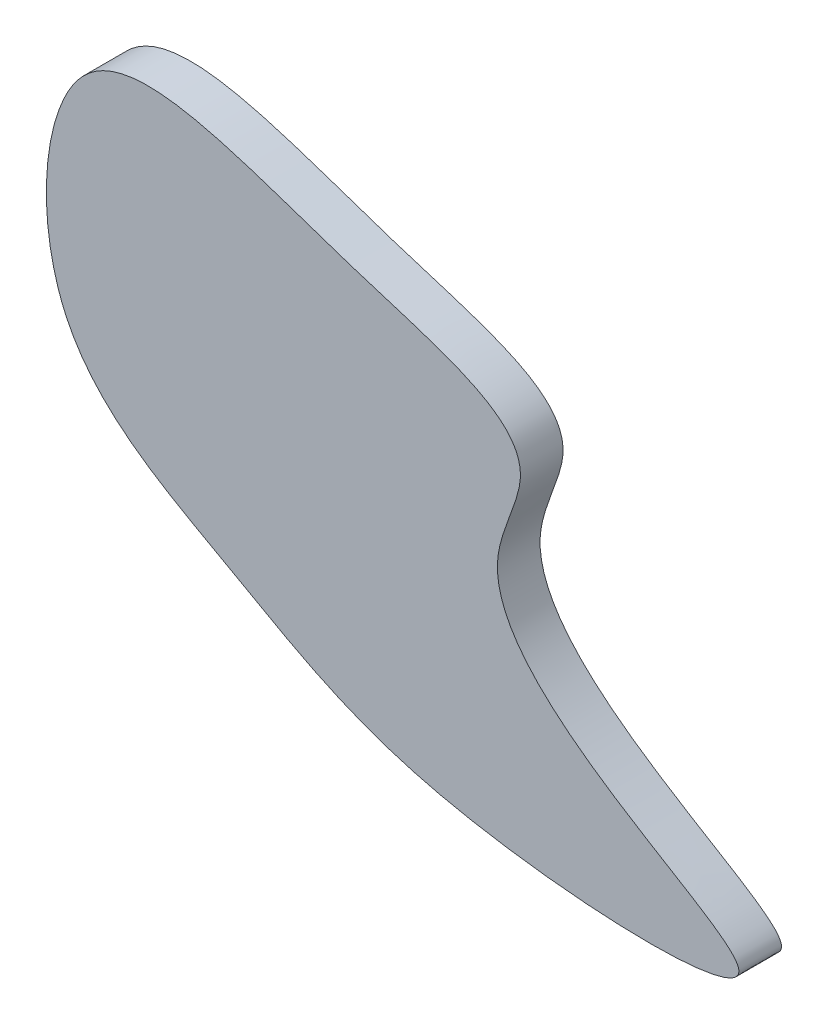
SolidWorks part; units mm, degrees
ref_plane "Ebene vorne" through (0, 0, 0) normal (0, 0, 1) x (1, 0, 0)
ref_plane "Ebene oben" through (0, 0, 0) normal (0, 1, 0) x (1, 0, 0)
ref_plane "Ebene rechts" through (0, 0, 0) normal (1, 0, 0) x (0, 0, -1)
sketch "Skizze1" plane through (0, 0, 0) normal (0, 0, 1) x (1, 0, 0)
  spline S0 degree 3 poles (-83.5489, 88.8453) (-90.1612, 8.9211) (-39.7738, -16.2047) (0.6608, -42.2798) (127.9625, -47.4058) (3.665, -3.739) (35.3577, 46.6963) (-22.526, 60.0214) (-83.5489, 88.8453) (-90.1612, 8.9211) (-39.7738, -16.2047) knots -0.370338 -0.269275 -0.118235 0 0.112756 0.233476 0.401323 0.583683 0.629662 0.730725 0.881765 1 1.112756 1.233476 1.401323 only from (-80.5382, 16.1126) to (-80.5382, 16.1126)
extrude "Aufsatz-Linear austragen1" add sketch "Skizze1" along normal blind 10
sketch "Skizze2" plane through (0, 0, 0) normal (0, 0, 1) x (1, 0, 0)
  line L0 (82.0748, 0) -> (-87.8707, 0) construction
  line L1 (61.3555, 0) -> (61.3555, 82.8525) construction
sketch3d "3D-Skizze1"
  line L0 (77.0963, -42.6796, 0) -> (77.0963, 72.567, 0)
  line L1 (77.0963, 72.567, 0) -> (-85.2156, 72.567, 0)
  line L2 (-85.2156, 72.567, 0) -> (-85.2156, -42.6796, 0)
  line L3 (-85.2156, -42.6796, 0) -> (77.0963, -42.6796, 0)
  line L4 (77.0963, -42.6796, 10) -> (77.0963, 72.567, 10)
  line L5 (77.0963, 72.567, 10) -> (-85.2156, 72.567, 10)
  line L6 (-85.2156, 72.567, 10) -> (-85.2156, -42.6796, 10)
  line L7 (-85.2156, -42.6796, 10) -> (77.0963, -42.6796, 10)
  line L8 (77.0963, -42.6796, 0) -> (77.0963, -42.6796, 10)
  line L9 (77.0963, 72.567, 0) -> (77.0963, 72.567, 10)
  line L10 (-85.2156, 72.567, 0) -> (-85.2156, 72.567, 10)
  line L11 (-85.2156, -42.6796, 0) -> (-85.2156, -42.6796, 10)
